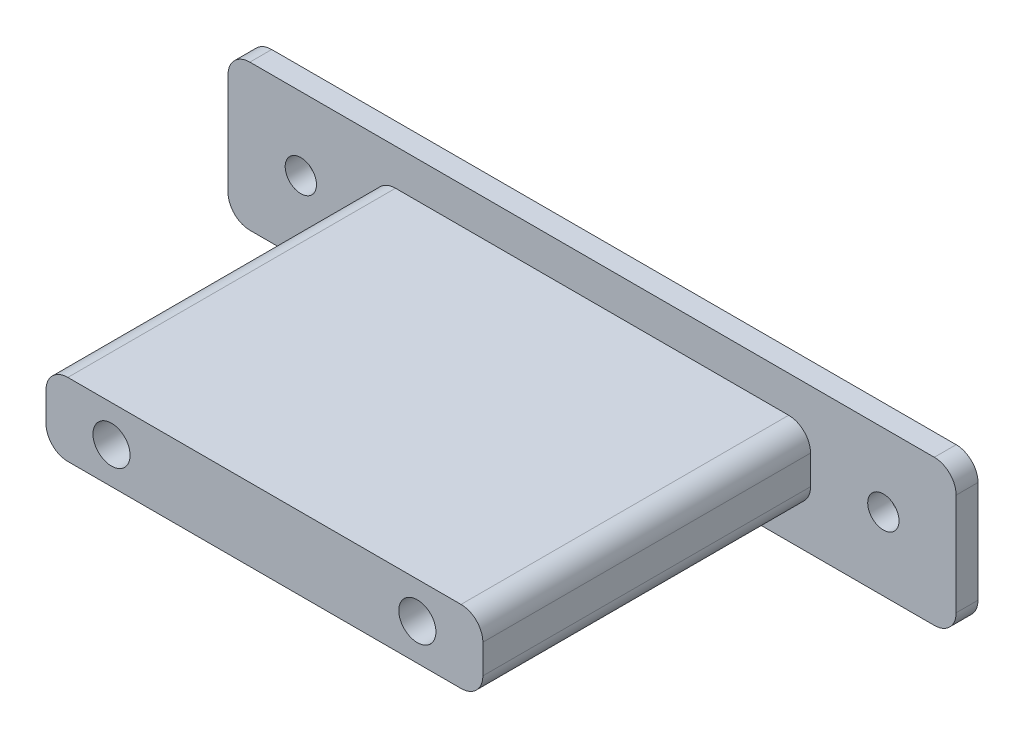
SolidWorks part; units mm, degrees
material "Balsa"
ref_plane "前视基准面" through (0, 0, 0) normal (0, 0, 1) x (1, 0, 0)
ref_plane "上视基准面" through (0, 0, 0) normal (0, 1, 0) x (1, 0, 0)
ref_plane "右视基准面" through (0, 0, 0) normal (1, 0, 0) x (0, 0, -1)
other "Configuration Table"
sketch "Sketch1" plane through (0, 0, 0) normal (0, 0, 1) x (1, 0, 0)
  line L0 (50, 0) -> (50, -20) construction
  line L1 (0, 0) -> (100, 0)
  line L2 (0, 0) -> (0, -20)
  line L3 (0, -20) -> (100, -20)
  line L4 (100, 0) -> (100, -20)
  circle A0 centre (10, -10) radius 2.15
  circle A2 centre (90, -10) radius 2.15
  circle A3 centre (29, -10) radius 2.55
  circle A4 centre (71, -10) radius 2.55
  point P12 (50, -20)
  point P14 (0, -10)
  dimension "D3" = 4.3
  dimension "D4" = 80
  dimension "D5" = 5.1
  dimension "D1" = 100
  dimension "D2" = 20
  dimension "D6" = 42
extrude "Boss-Extrude1" add sketch "Sketch1" along normal blind 3
sketch "Sketch2" plane through (0, 0, 3) normal (0, 0, 1) x (1, 0, 0)
  circle A0 centre (71, -10) radius 2.55 construction
  circle A1 centre (29, -10) radius 2.55 construction
  circle A2 centre (71, -10) radius 2.55
  circle A3 centre (29, -10) radius 2.55
extrude "Boss-Extrude3" add sketch "Sketch2" against normal up to surface (3 mm away) up to face at (50, -10, 0)
sketch "Sketch3" plane through (0, 0, 3) normal (0, 0, 1) x (1, 0, 0)
  line L0 (50, 33.818) -> (50, -33.818) construction
  line L1 (20, -5) -> (80, -5)
  line L2 (20, -5) -> (20, -15)
  line L3 (20, -15) -> (80, -15)
  line L4 (80, -5) -> (80, -15)
  line L7 (0, -10) -> (45.1082, -10) construction
  line L8 (100, 0) -> (0, 0) construction
  line L9 (0, 0) -> (0, -20) construction
  line L10 (100, 0) -> (0, 0)
  point P5 (22.5541, -10)
  point P11 (50, 0)
  point P14 (0, -10)
  point P15 (50, 0)
  dimension "D1" = 60
  dimension "D2" = 10
  dimension "D3" = 5
  dimension "D4" = 30
extrude "Boss-Extrude4" add sketch "Sketch3" along normal blind 45 contours L4 L1 L2 L3
sketch "Sketch4" plane through (0, 0, 48) normal (0, 0, 1) x (1, 0, 0)
  line L4 (100, 0) -> (0, 0)
  line L5 (100, -20) -> (100, 0)
  line L6 (0, -20) -> (100, -20)
  line L7 (0, 0) -> (0, -20)
  line L8 (100, 0) -> (0, 0)
  line L9 (100, -20) -> (100, 0)
  line L10 (0, -20) -> (100, -20)
  line L11 (0, 0) -> (0, -20)
  circle A1 centre (71, -10) radius 2.55
  circle A2 centre (71, -10) radius 2.55
  circle A3 centre (90, -10) radius 2.15
  circle A4 centre (90, -10) radius 2.15
  circle A5 centre (10, -10) radius 2.15
  circle A6 centre (10, -10) radius 2.15
  circle A7 centre (29, -10) radius 2.55
  circle A8 centre (29, -10) radius 2.55
  dimension "D1" = 0
  dimension "D2" = 0
  dimension "D3" = 0
  dimension "D4" = 0
  dimension "D5" = 0
extrude "Cut-Extrude3" cut sketch "Sketch4" against normal blind 8 contours A2 | A8
fillet "Fillet1" radius 3 8 edges at (0, 0, 1.5) (100, 0, 1.5) (100, -20, 1.5) (0, -20, 1.5) (80, -5, 25.5) (80, -15, 25.5) (20, -5, 25.5) (20, -15, 25.5)
